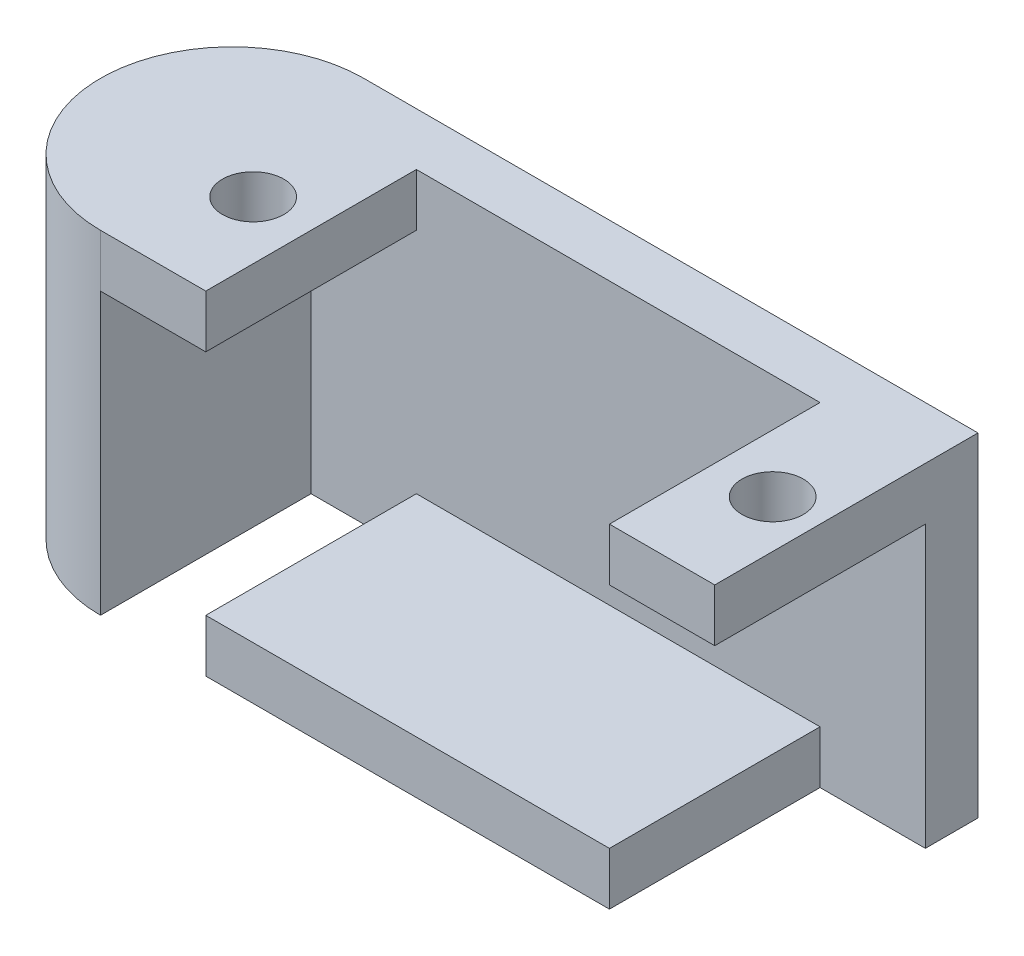
SolidWorks part; units mm, degrees
ref_plane "Plan de face" through (0, 0, 0) normal (0, 0, 1) x (1, 0, 0)
ref_plane "Plan de dessus" through (0, 0, 0) normal (0, 1, 0) x (1, 0, 0)
ref_plane "Plan de droite" through (0, 0, 0) normal (1, 0, 0) x (0, 0, -1)
sketch "Esquisse1" plane through (0, 0, 0) normal (0, 1, 0) x (1, 0, 0)
  line L1 (0, 0) -> (35, 0)
  line L3 (0, 15) -> (35, 15)
  line L4 (35, 0) -> (35, 15)
  arc A0 (0, 15) -> (0, 0) centre (0, 7.5) ccw
  dimension "D1" = 35
  dimension "D2" = 15
extrude "Boss.-Extru.1" add sketch "Esquisse1" along normal blind 19
sketch "Esquisse3" plane through (0, 0, 0) normal (0, 0, 1) x (1, 0, 0)
  line L0 (0, 19) -> (35, 19) construction
  line L1 (6, 19) -> (29, 19)
  line L2 (6, 19) -> (6, 16)
  line L3 (6, 3) -> (29, 3)
  line L4 (29, 19) -> (29, 16)
  line L5 (35, 19) -> (35, 0) construction
  line L6 (29, 16) -> (35, 16)
  line L8 (35, 3.1448) -> (35, 0)
  line L9 (35, 16) -> (35, 3.1448)
  line L10 (35, 0) -> (29, 0)
  line L13 (6, 16) -> (0, 16)
  line L14 (0, 3.8248) -> (0, 16)
  line L15 (0, 0) -> (35, 0) construction
  line L16 (29, 0) -> (29, 3)
  line L17 (6, 3) -> (6, 0)
  line L18 (6, 0) -> (0, 0)
  line L19 (0, 0) -> (0, 3.8248)
  dimension "D1" = 23
  dimension "D2" = 6
  dimension "D3" = 6
  dimension "D4" = 3
  dimension "D5" = 3
  dimension "D6" = 3
  dimension "D8" = 23
  dimension "D9" = 6
extrude "Enlèv. mat.-Extru.2" cut sketch "Esquisse3" against normal blind 12
sketch "Esquisse4" plane through (0, 19, 0) normal (0, 1, 0) x (1, 0, 0)
  line L0 (29, 0) -> (35, 0) construction
  line L1 (0, 0) -> (6, 0) construction
  line L3 (29, 12) -> (29, 0) construction
  line L4 (6, 12) -> (6, 0) construction
  circle A0 centre (32.3, 6) radius 1.75
  circle A1 centre (2.7, 6) radius 1.75
  point P10 (6, 6)
  dimension "D1" = 6
  dimension "D2" = 6
  dimension "D3" = 3.5
  dimension "D4" = 3.5
  dimension "D5" = 3.3
  dimension "D6" = 3.3
extrude "Enlèv. mat.-Extru.3" cut sketch "Esquisse4" against normal blind 12
sketch "Esquisse5" plane through (0, 0, 0) normal (0, -1, 0) x (1, 0, 0)
  line L0 (6, 0) -> (29, 0) construction
  line L3 (35, -12) -> (35, -15) construction
  line L4 (29, -12) -> (29, 0) construction
  circle A0 centre (23, -6) radius 1.25
  point P8 (35, -13.5)
  dimension "D1" = 2.5
  dimension "D2" = 6
  dimension "D3" = 6
extrude "Boss.-Extru.2" add sketch "Esquisse5" along normal blind 3
